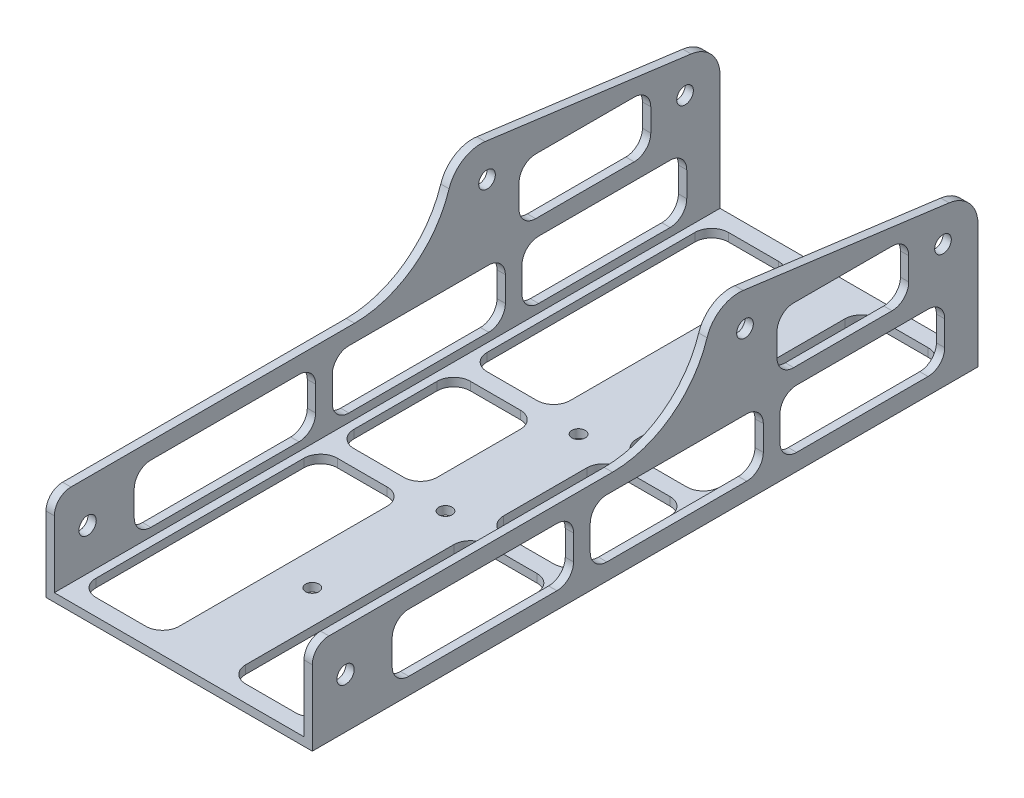
SolidWorks part; units mm, degrees
ref_plane "Front Plane" through (0, 0, 0) normal (0, 0, 1) x (1, 0, 0)
ref_plane "Top Plane" through (0, 0, 0) normal (0, 1, 0) x (1, 0, 0)
ref_plane "Right Plane" through (0, 0, 0) normal (1, 0, 0) x (0, 0, -1)
sketch "Sketch1" plane through (0, 0, 0) normal (0, 0, 1) x (1, 0, 0)
  line L0 (0, 0) -> (0, 73.025)
  line L1 (0, 73.025) -> (3.175, 73.025)
  line L2 (3.175, 73.025) -> (3.175, 3.175)
  line L3 (3.175, 3.175) -> (98.425, 3.175)
  line L4 (98.425, 3.175) -> (98.425, 73.025)
  line L5 (98.425, 73.025) -> (101.6, 73.025)
  line L6 (101.6, 73.025) -> (101.6, 0)
  line L7 (101.6, 0) -> (0, 0)
  dimension "D1" = 3.175
  dimension "D2" = 3.175
  dimension "D3" = 3.175
  dimension "D4" = 101.6
  dimension "D5" = 69.85
  dimension "D6" = 69.85
extrude "Boss-Extrude1" add sketch "Sketch1" along normal blind 254
sketch "Sketch2" plane through (101.6, 0, 0) normal (1, 0, 0) x (0, 0, -1)
  line L0 (-254, 0) -> (-254, 73.025) construction
  line L1 (-254, 0) -> (0, 0) construction
  circle A0 centre (-241.3, 19.05) radius 3.302
  circle A1 centre (-88.9, 57.15) radius 3.175
  dimension "D1" = 6.604
  dimension "D4" = 6.35
  dimension "D2" = 152.4
  dimension "D3" = 12.7
  dimension "D5" = 19.05
  dimension "D6" = 57.15
extrude "Cut-Extrude1" cut sketch "Sketch2" against normal blind 203.2
sketch "Sketch3" plane through (0, 3.175, 0) normal (0, 1, 0) x (1, 0, 0)
  line L2 (98.425, 0) -> (3.175, 0) construction
  line L4 (50.8, 0) -> (50.8, -254) construction
  line L5 (98.425, -254) -> (3.175, -254) construction
  circle A0 centre (50.8, -50.8) radius 2.54
  circle A1 centre (50.8, -101.6) radius 2.54
  circle A2 centre (50.8, -152.4) radius 2.54
  circle A3 centre (50.8, -203.2) radius 2.54
  dimension "D1" = 5.08
  dimension "D2" = 50.8
  dimension "D5" = 50.8
  dimension "D3" = 50.8
  dimension "D4" = 50.8
extrude "Cut-Extrude2" cut sketch "Sketch3" against normal blind 9.525
sketch "Sketch4" plane through (101.6, 0, 0) normal (1, 0, 0) x (0, 0, -1)
  line L1 (-254, 73.025) -> (-101.6, 73.025)
  line L2 (-254, 73.025) -> (-254, 34.925)
  line L3 (-254, 34.925) -> (-139.446, 34.925)
  line L4 (-101.6, 73.025) -> (-101.6, 72.771)
  arc A0 (-139.446, 34.925) -> (-101.6, 72.771) centre (-139.446, 72.771) ccw
  dimension "D3" = 37.846
  dimension "D1" = 38.1
  dimension "D2" = 152.4
extrude "Cut-Extrude3" cut sketch "Sketch4" against normal through all
sketch "Sketch5" plane through (0, 0, 0) normal (-1, 0, 0) x (0, 0, 1)
  line L0 (88.9, 57.15) -> (13.3519, 47.2039) construction
  line L1 (88.9, 57.15) -> (0, 57.15) construction
  line L2 (0, 73.025) -> (0, 0) construction
  circle A0 centre (88.9, 57.15) radius 3.175 construction
  circle A3 centre (88.9, 57.15) radius 3.175
  circle A4 centre (13.3519, 47.2039) radius 3.175
  dimension "D3" = 7.5
  dimension "D2" = 76.2
extrude "Cut-Extrude4" cut sketch "Sketch5" against normal through all contours A4
sketch "Sketch6" plane through (0, 0, 0) normal (-1, 0, 0) x (0, 0, 1)
  line L0 (13.3519, 47.2039) -> (88.9, 57.15) construction
  line L1 (11.6942, 59.7953) -> (117.2593, 73.6932)
  line L2 (11.6942, 59.7953) -> (-12.4817, 56.6124)
  line L3 (-12.4817, 56.6124) -> (-7.0221, 78.936)
  line L4 (-7.0221, 78.936) -> (117.2593, 83.6489)
  line L5 (117.2593, 83.6489) -> (117.2593, 62.8772)
  line L6 (11.6942, 59.7953) -> (87.2423, 69.7413) construction
  arc M4 (139.446, 34.925) -> (101.6, 72.771) centre (139.446, 72.771) cw
  line M5 (101.6, 72.771) -> (101.6, 73.025)
  line M6 (101.6, 73.025) -> (0, 73.025)
  line M7 (0, 73.025) -> (0, 0)
  dimension "D1" = 12.7
extrude "Cut-Extrude6" cut sketch "Sketch6" against normal through all contours L5 L4 L3 L2 L1 M7 M6 M5 M4 | L2 L1 M4 M5 M6 M7
fillet "Fillet1" radius 12.7 4 edges at (100.0125, 58.2557, 0) (1.5875, 58.2557, 0) (100.0125, 71.6338, 101.6171) (1.5875, 71.6338, 101.6171)
fillet "Fillet2" radius 6.35 2 edges at (100.0125, 34.925, 254) (1.5875, 34.925, 254)
sketch "Sketch7" plane through (0, 0, 0) normal (-1, 0, 0) x (0, 0, 1)
  line L0 (19.05, 6.35) -> (69.215, 6.35)
  line L1 (12.7, 12.7) -> (12.7, 22.225)
  line L2 (217.17, 28.575) -> (160.655, 28.575)
  line L3 (223.52, 22.225) -> (223.52, 12.7)
  line L4 (70.3422, 56.2887) -> (32.7762, 56.2887)
  line L5 (254, 0) -> (254, 28.575)
  line L6 (247.65, 34.925) -> (139.446, 34.925)
  line L7 (89.6162, 70.0539) -> (11.0423, 59.7094)
  line L8 (0, 47.1181) -> (0, 0)
  line L9 (0, 0) -> (254, 0)
  line L10 (254, 0) -> (254, 28.575)
  line L11 (247.65, 34.925) -> (139.446, 34.925)
  line L12 (89.6162, 70.0539) -> (11.0423, 59.7094)
  line L13 (0, 47.1181) -> (0, 0)
  line L14 (0, 0) -> (254, 0)
  line L15 (70.3422, 34.925) -> (32.7762, 34.925)
  line L16 (26.4262, 49.9387) -> (26.4262, 41.275)
  line L17 (76.6922, 49.9387) -> (76.6922, 41.275)
  line L18 (88.265, 6.35) -> (141.605, 6.35)
  line L20 (160.655, 6.35) -> (217.17, 6.35)
  line L21 (223.52, 34.925) -> (6.35, 34.925) construction
  line L22 (75.565, 22.225) -> (75.565, 12.7)
  line L23 (147.955, 22.225) -> (147.955, 12.7)
  line L24 (81.915, 22.225) -> (81.915, 12.7)
  line L25 (154.305, 22.225) -> (154.305, 12.7)
  line L26 (69.215, 28.575) -> (19.05, 28.575)
  line L27 (141.605, 28.575) -> (88.265, 28.575)
  line L28 (223.52, 28.575) -> (6.35, 28.575) construction
  circle A0 centre (13.3519, 47.2039) radius 3.175 construction
  circle A1 centre (13.3519, 47.2039) radius 3.175
  circle A2 centre (88.9, 57.15) radius 3.175 construction
  circle A3 centre (88.9, 57.15) radius 3.175
  arc A4 (254, 28.575) -> (247.65, 34.925) centre (247.65, 28.575) ccw
  arc A5 (103.3775, 61.3089) -> (139.446, 34.925) centre (139.446, 72.771) ccw
  arc A6 (103.3775, 61.3089) -> (89.6162, 70.0539) centre (91.2739, 57.4625) ccw
  arc A7 (11.0423, 59.7094) -> (0, 47.1181) centre (12.7, 47.1181) ccw
  arc A8 (254, 28.575) -> (247.65, 34.925) centre (247.65, 28.575) ccw
  arc A9 (103.3775, 61.3089) -> (139.446, 34.925) centre (139.446, 72.771) ccw
  arc A10 (103.3775, 61.3089) -> (89.6162, 70.0539) centre (91.2739, 57.4625) ccw
  arc A11 (11.0423, 59.7094) -> (0, 47.1181) centre (12.7, 47.1181) ccw
  circle A12 centre (13.3519, 47.2039) radius 12.7
  circle A13 centre (88.9, 57.15) radius 12.7
  circle A14 centre (241.3, 19.05) radius 12.7
  arc A15 (70.3422, 34.925) -> (76.6922, 41.275) centre (70.3422, 41.275) ccw
  arc A16 (76.6922, 49.9387) -> (70.3422, 56.2887) centre (70.3422, 49.9387) ccw
  arc A17 (26.4262, 49.9387) -> (32.7762, 56.2887) centre (32.7762, 49.9387) cw
  arc A18 (26.4262, 41.275) -> (32.7762, 34.925) centre (32.7762, 41.275) ccw
  arc A19 (217.17, 6.35) -> (223.52, 12.7) centre (217.17, 12.7) ccw
  arc A20 (217.17, 28.575) -> (223.52, 22.225) centre (217.17, 22.225) cw
  arc A21 (154.305, 22.225) -> (160.655, 28.575) centre (160.655, 22.225) cw
  arc A22 (154.305, 12.7) -> (160.655, 6.35) centre (160.655, 12.7) ccw
  arc A23 (147.955, 12.7) -> (141.605, 6.35) centre (141.605, 12.7) cw
  arc A24 (147.955, 22.225) -> (141.605, 28.575) centre (141.605, 22.225) ccw
  arc A25 (81.915, 22.225) -> (88.265, 28.575) centre (88.265, 22.225) cw
  arc A26 (81.915, 12.7) -> (88.265, 6.35) centre (88.265, 12.7) ccw
  arc A27 (19.05, 6.35) -> (12.7, 12.7) centre (19.05, 12.7) cw
  arc A28 (69.215, 6.35) -> (75.565, 12.7) centre (69.215, 12.7) ccw
  arc A29 (75.565, 22.225) -> (69.215, 28.575) centre (69.215, 22.225) ccw
  arc A30 (19.05, 28.575) -> (12.7, 22.225) centre (19.05, 22.225) ccw
  point P24 (91.1239, 58.6021)
  point P29 (12.55, 48.2577)
  point P47 (223.52, 6.35)
  point P73 (12.7, 6.35)
  dimension "D2" = 6.35
  dimension "D3" = 6.35
  dimension "D7" = 6.35
  dimension "D8" = 6.35
  dimension "D9" = 6.35
  dimension "D4" = 12.7
  dimension "8" = 210.82
  dimension "D1" = 0
  dimension "D6" = 6.35
extrude "Cut-Extrude7" cut sketch "Sketch7" against normal through all contours L16 A18 L15 A15 L17 A16 L4 A17 | L26 A30 L1 A27 L0 A28 L22 A29 | L24 A26 L18 A23 L23 A24 L27 A25 | L25 A22 L20 A19 L3 A20 L2 A21
sketch "Sketch8" plane through (0, 0, 0) normal (0, -1, 0) x (1, 0, 0)
  line L0 (12.7, 6.35) -> (31.75, 6.35)
  line L1 (95.25, 6.35) -> (95.25, 247.65)
  line L2 (95.25, 247.65) -> (50.8, 247.65)
  line L3 (6.35, 241.3) -> (6.35, 212.725)
  line L4 (0, 0) -> (101.6, 0)
  line L5 (101.6, 0) -> (101.6, 254)
  line L6 (101.6, 254) -> (0, 254)
  line L7 (0, 254) -> (0, 0)
  line L8 (0, 0) -> (101.6, 0)
  line L9 (101.6, 0) -> (101.6, 254)
  line L10 (101.6, 254) -> (0, 254)
  line L11 (0, 254) -> (0, 0)
  line L12 (38.1, 241.3) -> (38.1, 212.725)
  line L13 (50.8, 247.65) -> (50.8, 6.35) construction
  line L14 (50.8, 203.2) -> (38.1, 203.2)
  line L15 (50.8, 152.4) -> (38.1, 152.4)
  line L16 (50.8, 101.6) -> (38.1, 101.6)
  line L17 (50.8, 50.8) -> (38.1, 50.8)
  line L18 (31.75, 206.375) -> (12.7, 206.375)
  line L19 (50.8, 155.575) -> (38.5033, 155.575)
  line L20 (50.8, 104.775) -> (38.5033, 104.775)
  line L21 (50.8, 53.975) -> (38.5033, 53.975)
  line L22 (50.8, 200.025) -> (38.5033, 200.025)
  line L23 (50.8, 149.225) -> (38.5033, 149.225)
  line L24 (50.8, 98.425) -> (38.5033, 98.425)
  line L25 (50.8, 47.625) -> (38.5033, 47.625)
  line L26 (38.1, 193.675) -> (38.1, 161.925)
  line L27 (6.35, 193.675) -> (6.35, 161.925)
  line L28 (50.8, 203.2) -> (6.35, 203.2) construction
  line L29 (31.75, 200.025) -> (12.7, 200.025)
  line L30 (6.35, 247.65) -> (6.35, 6.35) construction
  line L31 (50.8, 206.375) -> (6.35, 206.375) construction
  line L32 (31.75, 247.65) -> (12.7, 247.65)
  line L33 (50.8, 200.025) -> (6.35, 200.025) construction
  line L34 (31.75, 155.575) -> (12.7, 155.575)
  line L35 (95.25, 247.65) -> (6.35, 247.65) construction
  line L36 (38.1, 142.875) -> (38.1, 111.125)
  line L37 (50.8, 155.575) -> (6.35, 155.575) construction
  line L38 (6.35, 142.875) -> (6.35, 111.125)
  line L39 (31.75, 149.225) -> (12.7, 149.225)
  line L40 (50.8, 152.4) -> (6.35, 152.4) construction
  line L41 (31.75, 104.775) -> (12.7, 104.775)
  line L42 (50.8, 149.225) -> (6.35, 149.225) construction
  line L43 (38.1, 92.075) -> (38.1, 60.325)
  line L44 (50.8, 104.775) -> (6.35, 104.775) construction
  line L45 (6.35, 92.075) -> (6.35, 60.325)
  line L46 (31.75, 98.425) -> (12.7, 98.425)
  line L47 (50.8, 101.6) -> (6.35, 101.6) construction
  line L48 (6.35, 41.275) -> (6.35, 12.7)
  line L49 (50.8, 98.425) -> (6.35, 98.425) construction
  line L50 (38.1, 41.275) -> (38.1, 12.7)
  line L51 (50.8, 50.8) -> (6.35, 50.8) construction
  line L52 (31.75, 53.975) -> (12.7, 53.975)
  line L53 (31.75, 47.625) -> (12.7, 47.625)
  line L54 (50.8, 53.975) -> (6.35, 53.975) construction
  line L55 (50.8, 6.35) -> (95.25, 6.35)
  line L56 (50.8, 47.625) -> (6.35, 47.625) construction
  line L57 (95.25, 41.275) -> (95.25, 12.7)
  line L58 (6.35, 6.35) -> (95.25, 6.35) construction
  line L59 (69.85, 47.625) -> (88.9, 47.625)
  line L60 (63.5, 41.275) -> (63.5, 12.7)
  line L61 (88.9, 6.35) -> (69.85, 6.35)
  line L62 (69.85, 98.425) -> (88.9, 98.425)
  line L63 (63.5, 92.075) -> (63.5, 60.325)
  line L64 (69.85, 53.975) -> (88.9, 53.975)
  line L65 (95.25, 92.075) -> (95.25, 60.325)
  line L66 (69.85, 149.225) -> (88.9, 149.225)
  line L67 (63.5, 142.875) -> (63.5, 111.125)
  line L68 (69.85, 104.775) -> (88.9, 104.775)
  line L69 (95.25, 142.875) -> (95.25, 111.125)
  line L70 (69.85, 200.025) -> (88.9, 200.025)
  line L71 (63.5, 193.675) -> (63.5, 161.925)
  line L72 (69.85, 155.575) -> (88.9, 155.575)
  line L73 (95.25, 193.675) -> (95.25, 161.925)
  line L74 (69.85, 247.65) -> (88.9, 247.65)
  line L75 (63.5, 241.3) -> (63.5, 212.725)
  line L76 (69.85, 206.375) -> (88.9, 206.375)
  line L77 (95.25, 241.3) -> (95.25, 212.725)
  line L78 (6.35, 212.725) -> (6.35, 193.675)
  line L79 (38.1, 193.675) -> (38.1, 212.725)
  line L80 (6.35, 60.325) -> (6.35, 41.275)
  line L81 (38.1, 41.275) -> (38.1, 60.325)
  line L82 (63.5, 212.725) -> (63.5, 193.675)
  line L83 (95.25, 193.675) -> (95.25, 212.725)
  line L84 (63.5, 60.325) -> (63.5, 41.275)
  line L85 (95.25, 41.275) -> (95.25, 60.325)
  circle A0 centre (50.8, 203.2) radius 12.7
  circle A1 centre (50.8, 50.8) radius 2.54
  circle A2 centre (50.8, 50.8) radius 2.54
  circle A3 centre (50.8, 101.6) radius 2.54
  circle A4 centre (50.8, 101.6) radius 2.54
  circle A5 centre (50.8, 152.4) radius 2.54
  circle A6 centre (50.8, 152.4) radius 2.54
  circle A7 centre (50.8, 203.2) radius 2.54
  circle A8 centre (50.8, 203.2) radius 2.54
  circle A9 centre (50.8, 152.4) radius 12.7
  circle A10 centre (50.8, 101.6) radius 12.7
  circle A11 centre (50.8, 50.8) radius 12.7
  arc A12 (12.7, 6.35) -> (6.35, 12.7) centre (12.7, 12.7) cw
  arc A13 (38.1, 12.7) -> (31.75, 6.35) centre (31.75, 12.7) cw
  arc A14 (38.1, 41.275) -> (31.75, 47.625) centre (31.75, 41.275) ccw
  arc A15 (12.7, 47.625) -> (6.35, 41.275) centre (12.7, 41.275) ccw
  arc A16 (38.1, 92.075) -> (31.75, 98.425) centre (31.75, 92.075) ccw
  arc A17 (12.7, 98.425) -> (6.35, 92.075) centre (12.7, 92.075) ccw
  arc A18 (6.35, 111.125) -> (12.7, 104.775) centre (12.7, 111.125) ccw
  arc A19 (31.75, 104.775) -> (38.1, 111.125) centre (31.75, 111.125) ccw
  arc A20 (38.1, 142.875) -> (31.75, 149.225) centre (31.75, 142.875) ccw
  arc A21 (12.7, 149.225) -> (6.35, 142.875) centre (12.7, 142.875) ccw
  arc A22 (6.35, 161.925) -> (12.7, 155.575) centre (12.7, 161.925) ccw
  arc A23 (31.75, 155.575) -> (38.1, 161.925) centre (31.75, 161.925) ccw
  arc A24 (38.1, 193.675) -> (31.75, 200.025) centre (31.75, 193.675) ccw
  arc A25 (12.7, 200.025) -> (6.35, 193.675) centre (12.7, 193.675) ccw
  arc A26 (12.7, 206.375) -> (6.35, 212.725) centre (12.7, 212.725) cw
  arc A27 (38.1, 212.725) -> (31.75, 206.375) centre (31.75, 212.725) cw
  arc A28 (38.1, 241.3) -> (31.75, 247.65) centre (31.75, 241.3) ccw
  arc A29 (12.7, 247.65) -> (6.35, 241.3) centre (12.7, 241.3) ccw
  arc A30 (12.7, 53.975) -> (6.35, 60.325) centre (12.7, 60.325) cw
  arc A31 (38.1, 60.325) -> (31.75, 53.975) centre (31.75, 60.325) cw
  arc A32 (88.9, 47.625) -> (95.25, 41.275) centre (88.9, 41.275) cw
  arc A33 (63.5, 41.275) -> (69.85, 47.625) centre (69.85, 41.275) cw
  arc A34 (88.9, 6.35) -> (95.25, 12.7) centre (88.9, 12.7) ccw
  arc A35 (63.5, 12.7) -> (69.85, 6.35) centre (69.85, 12.7) ccw
  arc A36 (63.5, 92.075) -> (69.85, 98.425) centre (69.85, 92.075) cw
  arc A37 (63.5, 60.325) -> (69.85, 53.975) centre (69.85, 60.325) ccw
  arc A38 (88.9, 98.425) -> (95.25, 92.075) centre (88.9, 92.075) cw
  arc A39 (88.9, 53.975) -> (95.25, 60.325) centre (88.9, 60.325) ccw
  arc A40 (63.5, 142.875) -> (69.85, 149.225) centre (69.85, 142.875) cw
  arc A41 (69.85, 104.775) -> (63.5, 111.125) centre (69.85, 111.125) cw
  arc A42 (95.25, 111.125) -> (88.9, 104.775) centre (88.9, 111.125) cw
  arc A43 (88.9, 149.225) -> (95.25, 142.875) centre (88.9, 142.875) cw
  arc A44 (63.5, 193.675) -> (69.85, 200.025) centre (69.85, 193.675) cw
  arc A45 (69.85, 155.575) -> (63.5, 161.925) centre (69.85, 161.925) cw
  arc A46 (95.25, 161.925) -> (88.9, 155.575) centre (88.9, 161.925) cw
  arc A47 (88.9, 200.025) -> (95.25, 193.675) centre (88.9, 193.675) cw
  arc A48 (63.5, 241.3) -> (69.85, 247.65) centre (69.85, 241.3) cw
  arc A49 (63.5, 212.725) -> (69.85, 206.375) centre (69.85, 212.725) ccw
  arc A50 (88.9, 206.375) -> (95.25, 212.725) centre (88.9, 212.725) ccw
  arc A51 (88.9, 247.65) -> (95.25, 241.3) centre (88.9, 241.3) cw
  point P74 (38.1, 47.625)
  point P80 (38.1, 98.425)
  point P91 (38.1, 149.225)
  point P102 (38.1, 200.025)
  point P113 (38.1, 247.65)
  point P122 (38.1, 53.975)
  dimension "D6" = 6.35
  dimension "1" = 25.4
  dimension "D9" = 6.35
  dimension "D10" = 6.35
  dimension "D7" = 3.175
  dimension "D1" = 0
  dimension "D2" = 0
  dimension "D3" = 0
  dimension "D4" = 0
  dimension "D5" = 0
  dimension "D8" = 3.175
extrude "Cut-Extrude8" cut sketch "Sketch8" against normal blind 116.332 contours L32 A29 L3 A26 L18 A27 L12 A28 | A51 L2 A48 L75 A49 L76 A50 L1 | L29 A25 L27 A22 L34 A23 L26 A24 | A47 L70 A44 L71 A45 L72 A46 L1 | L39 A21 L38 A18 L41 A19 L36 A20 | A43 L66 A40 L67 A41 L68 A42 L1 | A31 L43 A16 L46 A17 L45 A30 L52 | L64 A39 L1 A38 L62 A36 L63 A37 | L53 A15 L48 A12 L0 A13 L50 A14 | L60 A35 L55 A34 L1 A32 L59 A33 | L79 A27 L18 A26 L78 A25 L29 A24 | L81 A31 L52 A30 L80 A15 L53 A14 | A50 L76 A49 L82 A44 L70 A47 L1 | A39 L64 A37 L84 A33 L59 A32 L1
